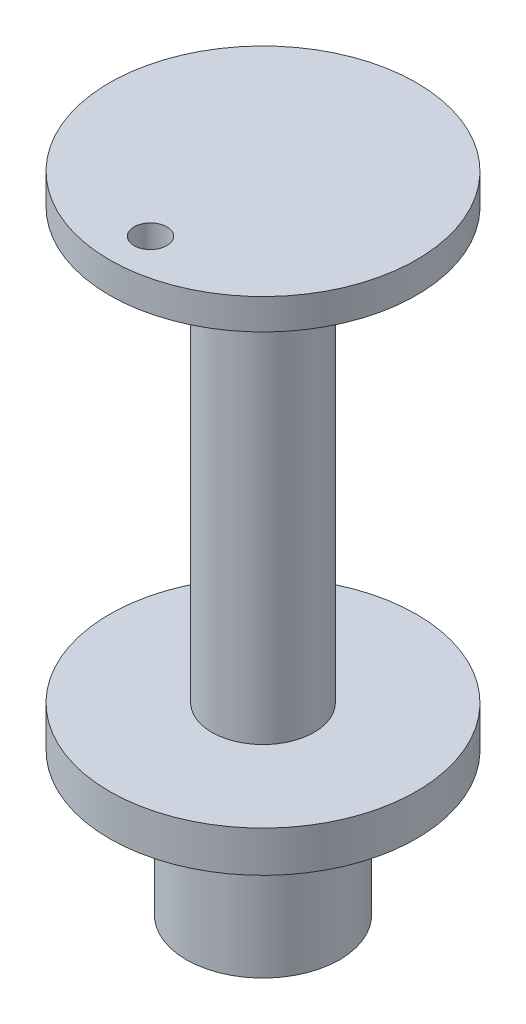
SolidWorks part; units mm, degrees
ref_plane "Front Plane" through (0, 0, 0) normal (0, 0, 1) x (1, 0, 0)
ref_plane "Top Plane" through (0, 0, 0) normal (0, 1, 0) x (1, 0, 0)
ref_plane "Right Plane" through (0, 0, 0) normal (1, 0, 0) x (0, 0, -1)
sketch "Sketch1" plane through (0, 0, 0) normal (0, 1, 0) x (1, 0, 0)
  line L0 (0, 16.8153) -> (0, -19.4467) construction
  line L1 (-24.1961, 0) -> (25.9931, 0) construction
  circle A0 centre (0, 0) radius 15
  dimension "D1" = 30
extrude "Boss-Extrude1" add sketch "Sketch1" along normal mid plane 4
sketch "Sketch2" plane through (0, -2, 0) normal (0, -1, 0) x (1, 0, 0)
  circle A0 centre (0, 0) radius 7.5
  circle A1 centre (0, 0) radius 6.3
  dimension "D1" = 15
  dimension "D2" = 1.2
extrude "Boss-Extrude2" add sketch "Sketch2" along normal blind 14
sketch "Sketch4" plane through (0, 2, 0) normal (0, 1, 0) x (1, 0, 0)
  circle A0 centre (0, 0) radius 5
  dimension "D1" = 10
extrude "Boss-Extrude3" add sketch "Sketch4" along normal blind 42
sketch "Sketch5" plane through (0, 44, 0) normal (0, 1, 0) x (1, 0, 0)
  circle A1 centre (0, 0) radius 15
  circle A2 centre (0, 0) radius 15
  dimension "D1" = 0
extrude "Boss-Extrude4" add sketch "Sketch5" along normal blind 3
sketch "Sketch6" plane through (0, 47, 0) normal (0, 1, 0) x (1, 0, 0)
  line L0 (0, 18.3534) -> (0, -22.1485) construction
  line L1 (-21.1434, 0) -> (30.8683, 0) construction
  circle A0 centre (0, -11) radius 1.6
  point P6 (0, -15)
  dimension "D1" = 3.2
  dimension "D2" = 4
extrude "Cut-Extrude1" cut sketch "Sketch6" against normal blind 3
